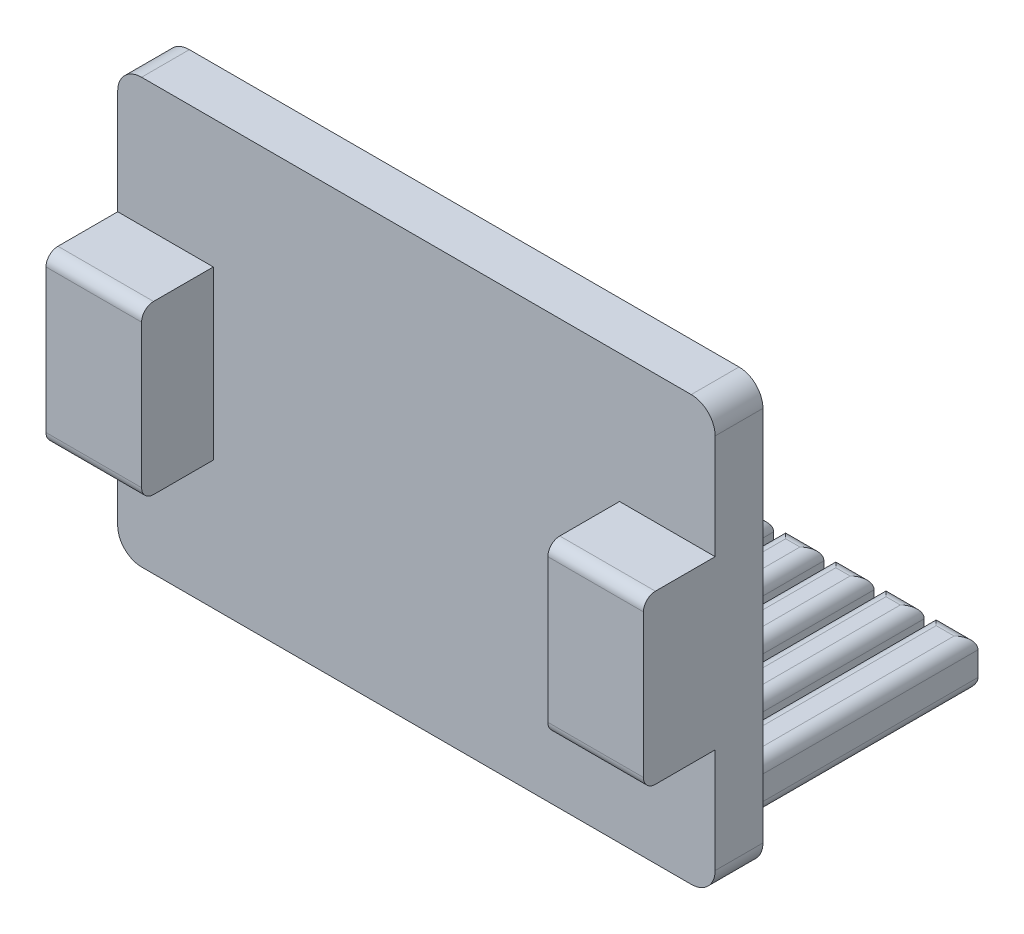
SolidWorks part; units mm, degrees
ref_plane "Front Plane" through (0, 0, 0) normal (0, 0, 1) x (1, 0, 0)
ref_plane "Top Plane" through (0, 0, 0) normal (0, 1, 0) x (1, 0, 0)
ref_plane "Right Plane" through (0, 0, 0) normal (1, 0, 0) x (0, 0, -1)
sketch "Sketch1" plane through (0, 0, 0) normal (0, 0, 1) x (1, 0, 0)
  line L0 (0, 0) -> (0, 17.75)
  line L1 (0, 17.75) -> (25, 17.75)
  line L2 (25, 17.75) -> (25, 0)
  line L3 (25, 0) -> (0, 0)
extrude "Boss-Extrude1" add sketch "Sketch1" along normal blind 2
sketch "Sketch2" plane through (0, 0, 2) normal (0, 0, 1) x (1, 0, 0)
  line L0 (0, 8.875) -> (0, 12.375)
  line L1 (25, 0) -> (25, 17.75) construction
  line L2 (21, 8.875) -> (21, 12.375)
  line L3 (21, 12.375) -> (25, 12.375)
  line L4 (25, 12.375) -> (25, 5.375)
  line L5 (25, 5.375) -> (21, 5.375)
  line L6 (21, 5.375) -> (21, 8.875)
  line L7 (0, 17.75) -> (0, 0) construction
  line L8 (0, 12.375) -> (4, 12.375)
  line L9 (4, 12.375) -> (4, 5.375)
  line L10 (4, 5.375) -> (0, 5.375)
  line L11 (0, 5.375) -> (0, 8.875)
extrude "Boss-Extrude2" add sketch "Sketch2" along normal blind 3
sketch "Sketch3" plane through (0, 0, 0) normal (0, 0, -1) x (-1, 0, 0)
  line L0 (-25, 0) -> (-25, 1) construction
  line L1 (-25, 0) -> (-25, 17.75) construction
  line L2 (-25, 1) -> (-24, 1) construction
  line L3 (-24, 1) -> (-24, 3)
  line L4 (-24, 3) -> (-1, 3)
  line L5 (-1, 3) -> (-1, 1)
  line L6 (-1, 1) -> (-24, 1)
extrude "Boss-Extrude3" add sketch "Sketch3" along normal blind 10
sketch "Sketch4" plane through (0, 0, -10) normal (0, 0, -1) x (-1, 0, 0)
  line L0 (-24, 2) -> (-1, 2) construction
  line L1 (-24, 3) -> (-24, 1) construction
  line L2 (-1, 1) -> (-1, 3) construction
  line L3 (-24, 2) -> (-22, 2) construction
  line L4 (-19.9, 3) -> (-20.15, 3)
  line L5 (-1, 3) -> (-24, 3) construction
  line L6 (-22, 3) -> (-22.25, 3)
  line L7 (-22.25, 3) -> (-22.25, 1)
  line L8 (-24, 1) -> (-1, 1) construction
  line L9 (-22.25, 1) -> (-21.75, 1)
  line L10 (-21.75, 1) -> (-21.75, 3)
  line L11 (-1, 3) -> (-24, 3) construction
  line L12 (-21.75, 3) -> (-22, 3)
  line L13 (-20.15, 3) -> (-20.15, 1)
  line L14 (-20.15, 1) -> (-19.65, 1)
  line L15 (-19.65, 1) -> (-19.65, 3)
  line L16 (-19.65, 3) -> (-19.9, 3)
  line L17 (-17.8, 3) -> (-18.05, 3)
  line L18 (-18.05, 3) -> (-18.05, 1)
  line L19 (-18.05, 1) -> (-17.55, 1)
  line L20 (-17.55, 1) -> (-17.55, 3)
  line L21 (-17.55, 3) -> (-17.8, 3)
  line L22 (-15.7, 3) -> (-15.95, 3)
  line L23 (-15.95, 3) -> (-15.95, 1)
  line L24 (-15.95, 1) -> (-15.45, 1)
  line L25 (-15.45, 1) -> (-15.45, 3)
  line L26 (-15.45, 3) -> (-15.7, 3)
  line L27 (-13.6, 3) -> (-13.85, 3)
  line L28 (-13.85, 3) -> (-13.85, 1)
  line L29 (-13.85, 1) -> (-13.35, 1)
  line L30 (-13.35, 1) -> (-13.35, 3)
  line L31 (-13.35, 3) -> (-13.6, 3)
  line L32 (-11.5, 3) -> (-11.75, 3)
  line L33 (-11.75, 3) -> (-11.75, 1)
  line L34 (-11.75, 1) -> (-11.25, 1)
  line L35 (-11.25, 1) -> (-11.25, 3)
  line L36 (-11.25, 3) -> (-11.5, 3)
  line L37 (-9.4, 3) -> (-9.65, 3)
  line L38 (-9.65, 3) -> (-9.65, 1)
  line L39 (-9.65, 1) -> (-9.15, 1)
  line L40 (-9.15, 1) -> (-9.15, 3)
  line L41 (-9.15, 3) -> (-9.4, 3)
  line L42 (-7.3, 3) -> (-7.55, 3)
  line L43 (-7.55, 3) -> (-7.55, 1)
  line L44 (-7.55, 1) -> (-7.05, 1)
  line L45 (-7.05, 1) -> (-7.05, 3)
  line L46 (-7.05, 3) -> (-7.3, 3)
  line L47 (-5.2, 3) -> (-5.45, 3)
  line L48 (-5.45, 3) -> (-5.45, 1)
  line L49 (-5.45, 1) -> (-4.95, 1)
  line L50 (-4.95, 1) -> (-4.95, 3)
  line L51 (-4.95, 3) -> (-5.2, 3)
  line L52 (-3.1, 3) -> (-3.35, 3)
  line L53 (-3.35, 3) -> (-3.35, 1)
  line L54 (-3.35, 1) -> (-2.85, 1)
  line L55 (-2.85, 1) -> (-2.85, 3)
  line L56 (-2.85, 3) -> (-3.1, 3)
  dimension "D1" = 10
extrude "Cut-Extrude1" cut sketch "Sketch4" against normal blind 8
fillet "Fillet1" radius 1 4 edges at (0, 17.75, 1) (0, 0, 1) (25, 0, 1) (25, 17.75, 1)
fillet "Fillet2" radius 0.5 90 edges at (1, 2, 0) (24, 2, 0) (22.25, 3, -6) (23.125, 3, -10) (24, 3, -5) (12.5, 3, 0) (1, 3, -5) (1.925, 3, -10) (2.85, 3, -6) (3.1, 3, -2) (3.35, 3, -6) (4.15, 3, -10) (4.95, 3, -6) (5.2, 3, -2) (5.45, 3, -6) (6.25, 3, -10) (7.05, 3, -6) (7.3, 3, -2) (7.55, 3, -6) (8.35, 3, -10) (9.15, 3, -6) (9.4, 3, -2) (9.65, 3, -6) (10.45, 3, -10) (11.25, 3, -6) (11.5, 3, -2) (11.75, 3, -6) (12.55, 3, -10) (13.35, 3, -6) (13.6, 3, -2) (13.85, 3, -6) (14.65, 3, -10) (15.45, 3, -6) (15.7, 3, -2) (15.95, 3, -6) (16.75, 3, -10) (17.55, 3, -6) (17.8, 3, -2) (18.05, 3, -6) (18.85, 3, -10) (19.65, 3, -6) (19.9, 3, -2) (20.15, 3, -6) (20.95, 3, -10) (21.75, 3, -6) (22, 3, -2) (20.15, 1, -6) (19.9, 1, -2) (19.65, 1, -6) (18.85, 1, -10) (18.05, 1, -6) (17.8, 1, -2) (17.55, 1, -6) (16.75, 1, -10) (15.95, 1, -6) (15.7, 1, -2) (15.45, 1, -6) (14.65, 1, -10) (13.85, 1, -6) (13.6, 1, -2) (13.35, 1, -6) (12.55, 1, -10) (11.75, 1, -6) (11.5, 1, -2) (11.25, 1, -6) (10.45, 1, -10) (9.65, 1, -6) (9.4, 1, -2) (9.15, 1, -6) (8.35, 1, -10) (7.55, 1, -6) (7.3, 1, -2) (7.05, 1, -6) (6.25, 1, -10) (5.45, 1, -6) (5.2, 1, -2) (4.95, 1, -6) (4.15, 1, -10) (3.35, 1, -6) (3.1, 1, -2) (2.85, 1, -6) (1.925, 1, -10) (1, 1, -5) (12.5, 1, 0) (24, 1, -5) (23.125, 1, -10) (22.25, 1, -6) (22, 1, -2) (21.75, 1, -6) (20.95, 1, -10)
fillet "Fillet3" radius 0.5 4 edges at (23, 12.375, 5) (23, 5.375, 5) (2, 5.375, 5) (2, 12.375, 5)
